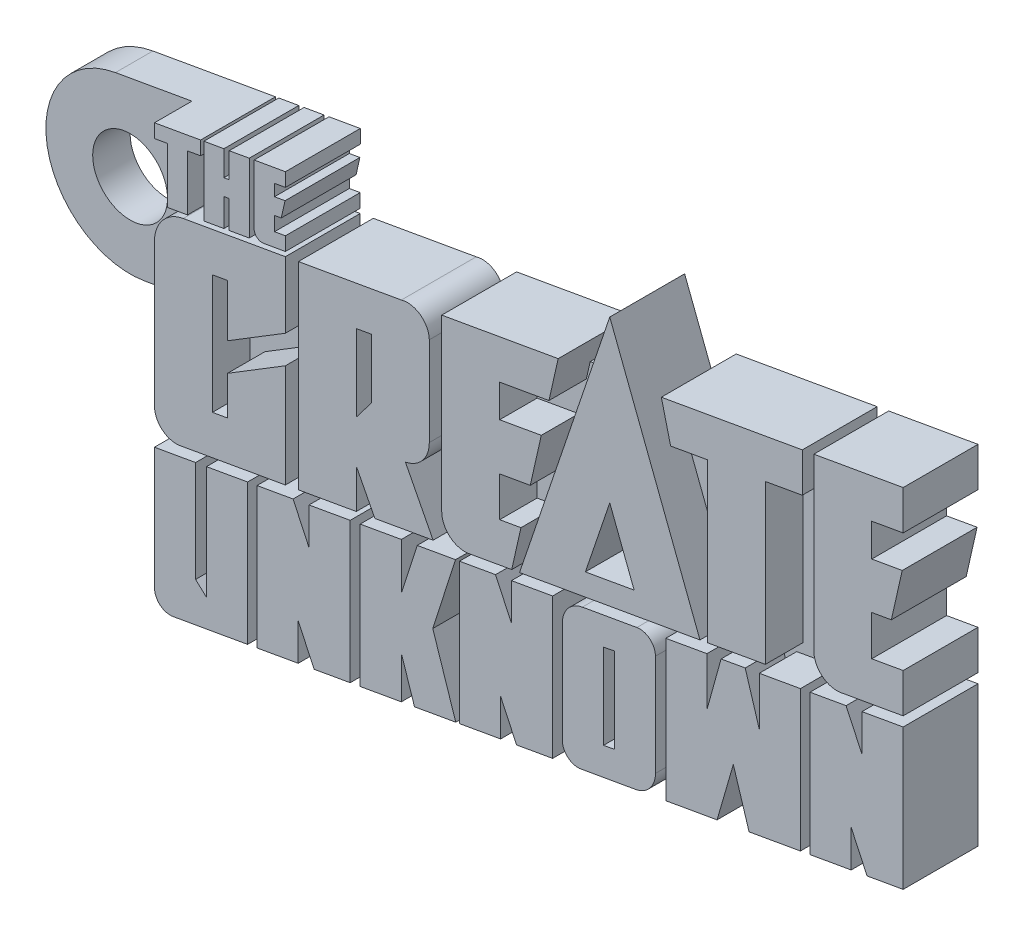
SolidWorks part; units mm, degrees
ref_plane "Front Plane" through (0, 0, 0) normal (0, 0, 1) x (1, 0, 0)
ref_plane "Top Plane" through (0, 0, 0) normal (0, 1, 0) x (1, 0, 0)
ref_plane "Right Plane" through (0, 0, 0) normal (1, 0, 0) x (0, 0, -1)
sketch "Sketch1" plane through (0, 0, 0) normal (0, 0, 1) x (1, 0, 0)
  line L165 (27.5388, 20.4964) -> (27.5388, 15.9483)
  line L166 (27.5388, 15.9483) -> (28.1244, 16.0637)
  line L167 (28.1244, 20.6118) -> (28.1244, 16.0637)
  line L168 (27.5388, 20.4964) -> (28.1244, 20.6118)
  line L169 (8.5269, 18.6309) -> (8.5269, 11.1151)
  line L170 (8.5269, 11.1151) -> (4.5441, 10.4128)
  line L171 (3.5529, 11.2445) -> (3.5529, 17.7538)
  line L172 (3.5529, 17.7538) -> (5.7478, 18.1409)
  line L173 (5.7478, 18.1409) -> (5.7478, 12.7317)
  line L174 (5.7478, 12.7317) -> (6.332, 12.1962)
  line L175 (6.332, 12.1962) -> (6.332, 18.2439)
  line L176 (6.332, 18.2439) -> (8.5269, 18.6309)
  line L177 (14.0078, 12.0815) -> (14.0078, 19.5973)
  line L178 (14.0078, 19.5973) -> (11.8102, 19.2098)
  line L179 (11.8102, 19.2098) -> (11.8102, 17.2332)
  line L180 (11.8102, 17.2332) -> (10.9586, 19.0597)
  line L181 (10.9586, 19.0597) -> (9.0322, 18.72)
  line L182 (9.0322, 18.72) -> (9.0322, 11.2042)
  line L183 (9.0322, 11.2042) -> (11.2298, 11.5917)
  line L184 (11.2298, 11.5917) -> (11.2298, 13.5683)
  line L185 (11.2298, 13.5683) -> (12.0815, 11.7418)
  line L186 (12.0815, 11.7418) -> (14.0078, 12.0815)
  line L187 (18.4217, 16.7978) -> (19.6355, 20.5896)
  line L188 (19.6355, 20.5896) -> (17.5898, 20.2289)
  line L189 (17.5898, 20.2289) -> (16.7417, 17.5794)
  line L190 (16.7417, 17.5794) -> (16.7417, 20.0794)
  line L191 (16.7417, 20.0794) -> (14.5441, 19.6919)
  line L192 (14.5441, 19.6919) -> (14.5441, 12.1761)
  line L193 (14.5441, 12.1761) -> (16.7417, 12.5636)
  line L194 (16.7417, 12.5636) -> (16.7417, 14.8199)
  line L195 (16.7417, 14.8199) -> (17.4448, 12.6875)
  line L196 (17.4448, 12.6875) -> (19.6489, 13.0762)
  line L197 (19.6489, 13.0762) -> (18.4217, 16.7978)
  line L198 (24.8245, 13.9888) -> (24.8245, 21.5046)
  line L199 (24.8245, 21.5046) -> (22.6269, 21.1171)
  line L200 (22.6269, 21.1171) -> (22.6269, 19.1405)
  line L201 (22.6269, 19.1405) -> (21.7752, 20.9669)
  line L202 (21.7752, 20.9669) -> (19.8489, 20.6273)
  line L203 (19.8489, 20.6273) -> (19.8489, 13.1115)
  line L204 (19.8489, 13.1115) -> (22.0465, 13.4989)
  line L205 (22.0465, 13.4989) -> (22.0465, 15.4755)
  line L206 (22.0465, 15.4755) -> (22.8981, 13.6491)
  line L207 (22.8981, 13.6491) -> (24.8245, 13.9888)
  line L208 (30.3195, 16.0433) -> (30.3195, 21.467)
  line L209 (29.3282, 22.2987) -> (26.4129, 21.7847)
  line L210 (25.3438, 20.5106) -> (25.3438, 15.0869)
  line L211 (26.335, 14.2551) -> (29.2504, 14.7692)
  line L212 (35.1142, 23.319) -> (35.8668, 20.8571)
  line L213 (35.8668, 20.8571) -> (35.8668, 23.4517)
  line L214 (35.8668, 23.4517) -> (38.0646, 23.8392)
  line L215 (38.0646, 23.8392) -> (38.0646, 16.3234)
  line L216 (38.0646, 16.3234) -> (35.3221, 15.8398)
  line L217 (35.3221, 15.8398) -> (34.4792, 18.537)
  line L218 (34.4792, 18.537) -> (33.6114, 15.5382)
  line L219 (33.6114, 15.5382) -> (30.871, 15.055)
  line L220 (30.871, 15.055) -> (30.871, 22.5708)
  line L221 (30.871, 22.5708) -> (33.0688, 22.9583)
  line L222 (33.0688, 22.9583) -> (33.0688, 20.3638)
  line L223 (33.0688, 20.3638) -> (33.8253, 23.0917)
  line L224 (33.8253, 23.0917) -> (35.1142, 23.319)
  line L225 (38.5772, 16.4138) -> (38.5772, 23.9296)
  line L226 (38.5772, 23.9296) -> (40.5036, 24.2692)
  line L227 (40.5036, 24.2692) -> (41.3553, 22.4428)
  line L228 (41.3553, 22.4428) -> (41.3553, 24.4194)
  line L229 (41.3553, 24.4194) -> (43.5528, 24.8069)
  line L230 (43.5528, 24.8069) -> (43.5528, 17.2911)
  line L231 (43.5528, 17.2911) -> (41.6265, 16.9514)
  line L232 (41.6265, 16.9514) -> (40.7748, 18.7779)
  line L233 (40.7748, 18.7779) -> (40.7748, 16.8013)
  line L234 (40.7748, 16.8013) -> (38.5772, 16.4138)
  line L235 (38.782, 35.0448) -> (38.782, 25.9457)
  line L236 (43.5528, 25.321) -> (40.2256, 24.7343)
  line L237 (43.5528, 27.4205) -> (43.5528, 25.321)
  line L238 (41.8757, 27.1247) -> (43.5528, 27.4205)
  line L239 (41.8757, 29.2669) -> (41.8757, 27.1247)
  line L240 (42.9229, 29.4516) -> (41.8757, 29.2669)
  line L241 (43.5037, 32.0256) -> (42.9229, 29.4516)
  line L242 (41.8757, 31.7386) -> (43.5037, 32.0256)
  line L243 (41.8757, 33.4908) -> (41.8757, 31.7386)
  line L244 (43.5528, 33.7865) -> (41.8757, 33.4908)
  line L245 (43.5528, 35.886) -> (43.5528, 33.7865)
  line L246 (38.782, 35.0448) -> (43.5528, 35.886)
  line L247 (33.096, 23.4771) -> (33.096, 31.9427)
  line L248 (33.096, 31.9427) -> (31.1296, 31.596)
  line L249 (31.1296, 31.596) -> (30.6338, 33.6081)
  line L250 (30.6338, 33.6081) -> (38.1649, 34.936)
  line L251 (38.1649, 34.936) -> (38.1649, 32.8365)
  line L252 (38.1649, 32.8365) -> (36.1897, 32.4882)
  line L253 (36.1897, 32.4882) -> (36.1897, 24.0226)
  line L254 (36.1897, 24.0226) -> (33.096, 23.4771)
  line L255 (26.575, 23.4945) -> (27.8781, 27.3418)
  line L256 (27.8781, 27.3418) -> (29.1808, 23.954)
  line L257 (29.1808, 23.954) -> (26.575, 23.4945)
  line L258 (27.8781, 35.9396) -> (23.0573, 21.707)
  line L259 (23.0573, 21.707) -> (32.6975, 23.4069)
  line L260 (32.6975, 23.4069) -> (27.8781, 35.9396)
  line L261 (15.1429, 28.7771) -> (15.1429, 25.594)
  line L262 (15.1429, 25.594) -> (14.3363, 24.5351)
  line L263 (14.3363, 24.5351) -> (14.3363, 28.6349)
  line L264 (14.3363, 28.6349) -> (15.1429, 28.7771)
  line L265 (18.9009, 22.4401) -> (18.9009, 31.5392)
  line L266 (18.9009, 31.5392) -> (25.1218, 32.6361)
  line L267 (25.1218, 32.6361) -> (24.6284, 30.4496)
  line L268 (24.6284, 30.4496) -> (21.9947, 29.9852)
  line L269 (21.9947, 29.9852) -> (21.9947, 28.2446)
  line L270 (21.9947, 28.2446) -> (24.2193, 28.6369)
  line L271 (24.2193, 28.6369) -> (23.6304, 26.0272)
  line L272 (23.6304, 26.0272) -> (21.9947, 25.7388)
  line L273 (21.9947, 25.7388) -> (21.9947, 23.6192)
  line L274 (21.9947, 23.6192) -> (23.1323, 23.8198)
  line L275 (23.1323, 23.8198) -> (22.6388, 21.6333)
  line L276 (22.6388, 21.6333) -> (21.9947, 21.5197)
  line L277 (21.9947, 21.5197) -> (20.3446, 21.2287)
  line L278 (11.2426, 30.1889) -> (11.2426, 19.6238)
  line L279 (11.2426, 19.6238) -> (14.3363, 20.1693)
  line L280 (14.3363, 20.1693) -> (14.3363, 22.2688)
  line L281 (14.3363, 22.2688) -> (15.3279, 20.3441)
  line L282 (15.3279, 20.3441) -> (18.4403, 20.8929)
  line L283 (18.4403, 20.8929) -> (16.9577, 23.7709)
  line L284 (18.2366, 25.3109) -> (18.2366, 30.0662)
  line L285 (16.7417, 31.1585) -> (11.2426, 30.1889)
  line L286 (8.8762, 33.7042) -> (8.8762, 30.5234)
  line L287 (9.381, 30.0998) -> (10.5468, 30.3053)
  line L288 (10.5468, 30.3053) -> (10.5468, 31.0325)
  line L289 (10.5468, 31.0325) -> (9.9645, 30.9298)
  line L290 (9.9645, 30.9298) -> (9.9645, 31.6825)
  line L291 (9.9645, 31.6825) -> (10.3249, 31.7461)
  line L292 (10.3249, 31.7461) -> (10.5283, 32.6476)
  line L293 (10.5283, 32.6476) -> (9.9645, 32.5482)
  line L294 (9.9645, 32.5482) -> (9.9645, 33.1689)
  line L295 (9.9645, 33.1689) -> (10.5487, 33.2719)
  line L296 (10.5487, 33.2719) -> (10.5487, 33.9991)
  line L297 (10.5487, 33.9991) -> (8.8762, 33.7042)
  line L298 (6.1925, 33.231) -> (6.1925, 29.5376)
  line L299 (6.1925, 29.5376) -> (7.2626, 29.7262)
  line L300 (7.2626, 29.7262) -> (7.2626, 31.2058)
  line L301 (7.2626, 31.2058) -> (7.5462, 31.2558)
  line L302 (7.5462, 31.2558) -> (7.5462, 29.7762)
  line L303 (7.5462, 29.7762) -> (8.6163, 29.9649)
  line L304 (8.6163, 29.9649) -> (8.6163, 33.6584)
  line L305 (8.6163, 33.6584) -> (7.5462, 33.4697)
  line L306 (7.5462, 33.4697) -> (7.5462, 32.128)
  line L307 (7.5462, 32.128) -> (7.2626, 32.078)
  line L308 (7.2626, 32.078) -> (7.2626, 33.4197)
  line L309 (7.2626, 33.4197) -> (6.1925, 33.231)
  line L310 (4.2501, 32.1569) -> (4.2501, 29.1951)
  line L311 (4.2501, 29.1951) -> (5.3202, 29.3837)
  line L312 (5.3202, 29.3837) -> (5.3202, 32.3456)
  line L313 (5.3202, 32.3456) -> (6.0168, 32.4685)
  line L314 (6.0168, 32.4685) -> (6.0168, 33.2)
  line L315 (6.0168, 33.2) -> (3.5529, 32.7655)
  line L316 (3.5529, 32.7655) -> (3.5529, 32.034)
  line L317 (3.5529, 32.034) -> (4.2501, 32.1569)
  line L318 (3.5529, 19.6594) -> (3.5529, 27.2755)
  line L319 (5.0867, 29.1034) -> (10.5468, 30.0662)
  line L320 (10.5468, 30.0662) -> (10.5468, 26.5235)
  line L321 (10.5468, 26.5235) -> (7.453, 24.6277)
  line L322 (7.453, 24.6277) -> (7.453, 27.4212)
  line L323 (7.453, 27.4212) -> (6.6466, 27.279)
  line L324 (6.6466, 27.279) -> (6.6466, 20.9129)
  line L325 (6.6466, 20.9129) -> (7.453, 21.0551)
  line L326 (7.453, 21.0551) -> (7.453, 23.1225)
  line L327 (7.453, 23.1225) -> (10.5468, 25.0183)
  line L328 (10.5468, 25.0183) -> (10.5468, 19.5011)
  line L329 (10.5468, 19.5011) -> (4.9232, 18.5095)
  arc A12 (3.5529, 11.2445) -> (4.5441, 10.4128) centre (4.3975, 11.2445) ccw
  arc A13 (30.3195, 21.467) -> (29.3282, 22.2987) centre (29.4749, 21.467) ccw
  arc A14 (26.4129, 21.7847) -> (25.3438, 20.5106) centre (26.6375, 20.5106) ccw
  arc A15 (25.3438, 15.0869) -> (26.335, 14.2551) centre (26.1884, 15.0869) ccw
  arc A16 (29.2504, 14.7692) -> (30.3195, 16.0433) centre (29.0258, 16.0433) ccw
  arc A17 (38.782, 25.9457) -> (40.2256, 24.7343) centre (40.012, 25.9457) ccw
  arc A18 (18.9009, 22.4401) -> (20.3446, 21.2287) centre (20.131, 22.4401) ccw
  arc A19 (16.9577, 23.7709) -> (18.2366, 25.3109) centre (16.6699, 25.3109) ccw
  arc A20 (18.2366, 30.0662) -> (16.7417, 31.1585) centre (17.0693, 30.0378) ccw
  arc A21 (8.8762, 30.5234) -> (9.381, 30.0998) centre (9.3063, 30.5234) ccw
  arc A22 (5.0867, 29.1034) -> (3.5529, 27.2755) centre (5.4091, 27.2755) ccw
  arc A23 (3.5529, 19.6594) -> (4.9232, 18.5095) centre (4.7205, 19.6594) ccw
  point P2 (0, 0)
extrude "Boss-Extrude1" add sketch "Sketch1" along normal blind 2
sketch "Sketch3" plane through (0, 0, 0) normal (0, 0, -1) x (-1, 0, 0)
  line L0 (-38.5772, 16.4138) -> (-38.5772, 23.9296) construction
  line L1 (-7.5462, 32.9346) -> (-7.2626, 32.8846)
  line L2 (-6.629, 33.3079) -> (-6.629, 32.7729) construction
  line L3 (-4.2501, 31.7461) -> (-4.7852, 31.7461) construction
  line L4 (-41.3553, 24.4194) -> (-43.5528, 24.8069) construction
  line L5 (-43.5528, 24.8069) -> (-43.5528, 17.2911) construction
  line L6 (-43.5528, 17.2911) -> (-41.6265, 16.9514) construction
  line L7 (-41.6265, 16.9514) -> (-40.7748, 18.7779) construction
  line L8 (-40.7748, 18.7779) -> (-40.7748, 16.8013) construction
  line L9 (-40.7748, 16.8013) -> (-38.5772, 16.4138) construction
  line L10 (-38.0646, 23.8392) -> (-38.0646, 16.3234) construction
  line L11 (-38.0646, 16.3234) -> (-35.3221, 15.8398) construction
  line L12 (-35.3221, 15.8398) -> (-34.4792, 18.537) construction
  line L13 (-34.4792, 18.537) -> (-33.6114, 15.5382) construction
  line L14 (-33.6114, 15.5382) -> (-30.871, 15.055) construction
  line L15 (-30.871, 15.055) -> (-30.871, 22.5708) construction
  line L16 (-1.0316, 23.1821) -> (-3.5529, 23.6267)
  line L17 (0.5313, 32.0454) -> (-3.5529, 32.7655)
  line L18 (-0.2501, 27.6137) -> (-4.2501, 27.6137) construction
  line L19 (-4.2501, 32.1569) -> (-4.2501, 29.1951) construction
  line L23 (-25.3438, 20.5106) -> (-25.3438, 15.0869) construction
  line L24 (-26.335, 14.2551) -> (-29.2504, 14.7692) construction
  line L25 (-30.3195, 16.0433) -> (-30.3195, 21.467) construction
  line L27 (-19.8489, 20.6273) -> (-19.8489, 13.1115) construction
  line L28 (-19.8489, 13.1115) -> (-22.0465, 13.4989) construction
  line L29 (-22.0465, 13.4989) -> (-22.0465, 15.4755) construction
  line L30 (-22.0465, 15.4755) -> (-22.8981, 13.6491) construction
  line L31 (-22.8981, 13.6491) -> (-24.8245, 13.9888) construction
  line L32 (-24.8245, 13.9888) -> (-24.8245, 21.5046) construction
  line L37 (-14.5441, 19.6919) -> (-14.5441, 12.1761) construction
  line L38 (-14.5441, 12.1761) -> (-16.7417, 12.5636) construction
  line L39 (-16.7417, 12.5636) -> (-16.7417, 14.8199) construction
  line L40 (-16.7417, 14.8199) -> (-17.4448, 12.6875) construction
  line L41 (-17.4448, 12.6875) -> (-19.6489, 13.0762) construction
  line L42 (-19.6489, 13.0762) -> (-18.4217, 16.7978) construction
  line L48 (-9.0322, 18.72) -> (-9.0322, 11.2042) construction
  line L49 (-9.0322, 11.2042) -> (-11.2298, 11.5917) construction
  line L50 (-11.2298, 11.5917) -> (-11.2298, 13.5683) construction
  line L51 (-11.2298, 13.5683) -> (-12.0815, 11.7418) construction
  line L52 (-12.0815, 11.7418) -> (-14.0078, 12.0815) construction
  line L53 (-14.0078, 12.0815) -> (-14.0078, 19.5973) construction
  line L60 (-8.5269, 18.6309) -> (-8.5269, 11.1151) construction
  line L61 (-8.5269, 11.1151) -> (-4.5441, 10.4128) construction
  line L62 (-3.5529, 11.2445) -> (-3.5529, 17.7538) construction
  line L63 (-3.5529, 17.7538) -> (-5.7478, 18.1409) construction
  line L68 (-6.0168, 32.4685) -> (-6.0168, 33.2) construction
  line L69 (-6.0168, 33.2) -> (-3.5529, 32.7655) construction
  line L74 (-8.6163, 29.9649) -> (-8.6163, 33.6584) construction
  line L75 (-8.6163, 33.6584) -> (-7.5462, 33.4697) construction
  line L76 (-7.5462, 33.4697) -> (-7.5462, 32.128) construction
  line L78 (-7.2626, 32.078) -> (-7.2626, 33.4197) construction
  line L79 (-7.2626, 33.4197) -> (-6.1925, 33.231) construction
  line L80 (-6.1925, 33.231) -> (-6.1925, 29.5376) construction
  line L86 (-8.8762, 33.7042) -> (-8.8762, 30.5234) construction
  line L87 (-9.381, 30.0998) -> (-10.5468, 30.3053) construction
  line L88 (-10.5468, 30.3053) -> (-10.5468, 31.0325) construction
  line L89 (-10.5468, 31.0325) -> (-9.9645, 30.9298) construction
  line L90 (-9.9645, 30.9298) -> (-9.9645, 31.6825) construction
  line L91 (-9.9645, 31.6825) -> (-10.3249, 31.7461) construction
  line L92 (-10.3249, 31.7461) -> (-10.5283, 32.6476) construction
  line L93 (-10.5283, 32.6476) -> (-9.9645, 32.5482) construction
  line L94 (-9.9645, 32.5482) -> (-9.9645, 33.1689) construction
  line L95 (-9.9645, 33.1689) -> (-10.5487, 33.2719) construction
  line L96 (-10.5487, 33.2719) -> (-10.5487, 33.9991) construction
  line L97 (-10.5487, 33.9991) -> (-8.8762, 33.7042) construction
  line L101 (-3.5529, 19.6594) -> (-3.5529, 27.2755) construction
  line L102 (-5.0867, 29.1034) -> (-10.5468, 30.0662) construction
  line L103 (-10.5468, 30.0662) -> (-10.5468, 26.5235) construction
  line L111 (-16.7417, 31.1585) -> (-11.2426, 30.1889) construction
  line L112 (-11.2426, 30.1889) -> (-11.2426, 19.6238) construction
  line L119 (-5.3202, 31.3658) -> (-5.3202, 29.3837) construction
  line L120 (-25.3438, 15.3127) -> (-41.8757, 18.2277) construction
  line L121 (-18.9009, 31.5392) -> (-25.1218, 32.6361) construction
  line L122 (-25.1218, 32.6361) -> (-24.6284, 30.4496) construction
  line L133 (-18.9009, 22.4401) -> (-18.9009, 31.5392) construction
  line L134 (-32.6975, 23.4069) -> (-27.8781, 35.9396) construction
  line L135 (-27.8781, 35.9396) -> (-23.0573, 21.707) construction
  line L137 (-30.6338, 33.6081) -> (-38.1649, 34.936) construction
  line L138 (-38.1649, 34.936) -> (-38.1649, 32.8365) construction
  line L144 (-31.1296, 31.596) -> (-30.6338, 33.6081) construction
  line L145 (-38.782, 35.0448) -> (-43.5528, 35.886) construction
  line L146 (-43.5528, 35.886) -> (-43.5528, 33.7865) construction
  line L147 (-43.5528, 33.7865) -> (-41.8757, 33.4908) construction
  line L148 (-41.8757, 33.4908) -> (-41.8757, 31.7386) construction
  line L149 (-41.8757, 31.7386) -> (-43.5037, 32.0256) construction
  line L150 (-43.5037, 32.0256) -> (-42.9229, 29.4516) construction
  line L151 (-42.9229, 29.4516) -> (-41.8757, 29.2669) construction
  line L152 (-41.8757, 29.2669) -> (-41.8757, 27.1247) construction
  line L153 (-41.8757, 27.1247) -> (-43.5528, 27.4205) construction
  line L154 (-43.5528, 27.4205) -> (-43.5528, 25.321) construction
  line L155 (-43.5528, 25.321) -> (-40.2256, 24.7343) construction
  line L156 (-38.782, 35.0448) -> (-38.782, 25.9457) construction
  line L157 (-38.5772, 16.4138) -> (-38.5772, 17.6461)
  line L161 (-41.8757, 24.5112) -> (-43.5528, 24.8069)
  line L162 (-43.5528, 24.8069) -> (-43.5528, 17.2911)
  line L163 (-43.5528, 17.2911) -> (-41.6265, 16.9514)
  line L164 (-41.6265, 16.9514) -> (-40.7748, 18.7779)
  line L165 (-40.7748, 18.7779) -> (-40.7748, 16.8013)
  line L166 (-40.7748, 16.8013) -> (-38.5772, 16.4138)
  line L167 (-38.0646, 17.5557) -> (-38.0646, 16.3234)
  line L168 (-38.0646, 16.3234) -> (-35.3221, 15.8398)
  line L169 (-35.3221, 15.8398) -> (-34.4792, 18.537)
  line L170 (-34.4792, 18.537) -> (-33.6114, 15.5382)
  line L171 (-33.6114, 15.5382) -> (-30.871, 15.055)
  line L172 (-30.871, 15.055) -> (-30.871, 16.2873)
  line L180 (-25.3438, 15.3127) -> (-25.3438, 15.0869)
  line L181 (-26.335, 14.2551) -> (-29.2504, 14.7692)
  line L182 (-30.3195, 16.0433) -> (-30.3195, 16.19)
  line L184 (-19.8489, 14.3438) -> (-19.8489, 13.1115)
  line L185 (-19.8489, 13.1115) -> (-22.0465, 13.4989)
  line L186 (-22.0465, 13.4989) -> (-22.0465, 15.4755)
  line L187 (-22.0465, 15.4755) -> (-22.8981, 13.6491)
  line L188 (-22.8981, 13.6491) -> (-24.8245, 13.9888)
  line L189 (-24.8245, 13.9888) -> (-24.8245, 15.2211)
  line L194 (-14.5441, 13.4084) -> (-14.5441, 12.1761)
  line L195 (-14.5441, 12.1761) -> (-16.7417, 12.5636)
  line L196 (-16.7417, 12.5636) -> (-16.7417, 14.8199)
  line L197 (-16.7417, 14.8199) -> (-17.4448, 12.6875)
  line L198 (-17.4448, 12.6875) -> (-19.6489, 13.0762)
  line L199 (-19.6489, 13.0762) -> (-19.2648, 14.2408)
  line L205 (-9.0322, 12.4365) -> (-9.0322, 11.2042)
  line L206 (-9.0322, 11.2042) -> (-11.2298, 11.5917)
  line L207 (-11.2298, 11.5917) -> (-11.2298, 13.5683)
  line L208 (-11.2298, 13.5683) -> (-12.0815, 11.7418)
  line L209 (-12.0815, 11.7418) -> (-14.0078, 12.0815)
  line L210 (-14.0078, 12.0815) -> (-14.0078, 13.3138)
  line L217 (-8.5269, 12.3474) -> (-8.5269, 11.1151)
  line L218 (-8.5269, 11.1151) -> (-4.5441, 10.4128)
  line L219 (-3.5529, 11.2445) -> (-3.5529, 17.7538)
  line L220 (-3.5529, 17.7538) -> (-4.7852, 17.9711)
  line L225 (-6.0168, 32.6649) -> (-6.0168, 33.2)
  line L226 (-6.0168, 33.2) -> (-3.5529, 32.7655)
  line L231 (-8.6163, 33.1233) -> (-8.6163, 33.6584)
  line L232 (-8.6163, 33.6584) -> (-7.5462, 33.4697)
  line L233 (-7.5462, 33.4697) -> (-7.5462, 32.9346)
  line L235 (-7.2626, 32.8846) -> (-7.2626, 33.4197)
  line L236 (-7.2626, 33.4197) -> (-6.1925, 33.231)
  line L237 (-6.1925, 33.231) -> (-6.1925, 32.6959)
  line L243 (-8.8762, 33.7042) -> (-8.8762, 33.1691)
  line L244 (-9.9645, 30.2027) -> (-10.5468, 30.3053)
  line L245 (-10.5468, 30.3053) -> (-10.5468, 31.0325)
  line L246 (-10.5468, 31.0325) -> (-9.9645, 30.9298)
  line L247 (-9.9645, 30.9298) -> (-9.9645, 31.6825)
  line L248 (-9.9645, 31.6825) -> (-10.3249, 31.7461)
  line L249 (-10.3249, 31.7461) -> (-10.5283, 32.6476)
  line L250 (-10.5283, 32.6476) -> (-9.9645, 32.5482)
  line L251 (-9.9645, 32.5482) -> (-9.9645, 33.1689)
  line L252 (-9.9645, 33.1689) -> (-10.5487, 33.2719)
  line L253 (-10.5487, 33.2719) -> (-10.5487, 33.9991)
  line L254 (-10.5487, 33.9991) -> (-8.8762, 33.7042)
  line L258 (-3.5529, 19.6594) -> (-3.5529, 23.6267)
  line L259 (-9.9645, 29.9635) -> (-10.5468, 30.0662)
  line L260 (-10.5468, 30.0662) -> (-10.5468, 28.8339)
  line L268 (-16.7417, 31.1585) -> (-11.2426, 30.1889)
  line L269 (-11.2426, 30.1889) -> (-11.2426, 28.9566)
  line L278 (-18.9009, 31.5392) -> (-25.1218, 32.6361)
  line L279 (-25.1218, 32.6361) -> (-24.8322, 31.3528)
  line L290 (-18.9009, 30.3069) -> (-18.9009, 31.5392)
  line L291 (-29.3365, 32.147) -> (-27.8781, 35.9396)
  line L292 (-27.8781, 35.9396) -> (-26.4192, 31.6326)
  line L294 (-30.6338, 33.6081) -> (-38.1649, 34.936)
  line L295 (-38.1649, 34.936) -> (-38.1649, 33.7037)
  line L301 (-30.9248, 32.4271) -> (-30.6338, 33.6081)
  line L302 (-38.782, 35.0448) -> (-43.5528, 35.886)
  line L303 (-43.5528, 35.886) -> (-43.5528, 33.7865)
  line L304 (-43.5528, 33.7865) -> (-41.8757, 33.4908)
  line L305 (-41.8757, 33.4908) -> (-41.8757, 31.7386)
  line L306 (-41.8757, 31.7386) -> (-43.5037, 32.0256)
  line L307 (-43.5037, 32.0256) -> (-42.9229, 29.4516)
  line L308 (-42.9229, 29.4516) -> (-41.8757, 29.2669)
  line L309 (-41.8757, 29.2669) -> (-41.8757, 27.1247)
  line L310 (-41.8757, 27.1247) -> (-43.5528, 27.4205)
  line L311 (-43.5528, 27.4205) -> (-43.5528, 25.321)
  line L312 (-43.5528, 25.321) -> (-41.8757, 25.0252)
  line L313 (-38.782, 35.0448) -> (-38.782, 33.8125)
  line L314 (-41.8757, 34.358) -> (-9.9645, 28.7312) construction
  line L315 (-9.9645, 28.7312) -> (-9.9645, 33.361) construction
  line L316 (-9.9645, 33.361) -> (-4.7852, 32.4478) construction
  line L317 (-4.7852, 32.4478) -> (-4.7852, 11.6876) construction
  line L318 (-4.7852, 11.6876) -> (-25.3438, 15.3127) construction
  line L319 (-41.8757, 18.2277) -> (-41.8757, 34.358) construction
  line L320 (-30.871, 16.2873) -> (-30.3113, 16.1886)
  line L321 (-25.3438, 15.3127) -> (-24.8245, 15.2211)
  line L322 (-19.8489, 14.3438) -> (-19.2648, 14.2408)
  line L323 (-14.5441, 13.4084) -> (-14.0078, 13.3138)
  line L324 (-9.0322, 12.4365) -> (-8.5269, 12.3474)
  line L325 (-4.7852, 18.4936) -> (-4.7852, 17.9711)
  line L327 (-6.0168, 32.6649) -> (-6.1925, 32.6959)
  line L328 (-8.6163, 33.1233) -> (-8.8762, 33.1691)
  line L329 (-9.9645, 30.2027) -> (-9.9645, 29.9635)
  line L330 (-10.5468, 28.8339) -> (-11.2426, 28.9566)
  line L331 (-18.2272, 30.1881) -> (-18.9009, 30.3069)
  line L332 (-24.8322, 31.3528) -> (-26.4192, 31.6326)
  line L333 (-29.3365, 32.147) -> (-30.9248, 32.4271)
  line L334 (-38.782, 33.8125) -> (-38.1649, 33.7037)
  line L335 (-41.8757, 25.0252) -> (-41.8757, 24.5112)
  line L336 (-14.6099, 30.7826) -> (-14.6099, 29.5503) construction
  line L337 (-12.7842, 11.8658) -> (-12.7842, 13.0981) construction
  line L338 (-3.5529, 26.0088) -> (-4.7852, 26.0088) construction
  line L339 (-4.2501, 31.3658) -> (-5.3202, 31.3658) construction
  line L340 (-38.5772, 17.6461) -> (-38.0646, 17.5557)
  arc A0 (-26.335, 14.2551) -> (-25.3438, 15.0869) centre (-26.1884, 15.0869) ccw construction
  arc A1 (-30.3195, 16.0433) -> (-29.2504, 14.7692) centre (-29.0258, 16.0433) ccw construction
  arc A2 (-1.0316, 23.1821) -> (0.5313, 32.0454) centre (-0.2501, 27.6137) ccw
  circle A3 centre (-0.2501, 27.6137) radius 2
  arc A4 (-4.5441, 10.4128) -> (-3.5529, 11.2445) centre (-4.3975, 11.2445) ccw construction
  arc A6 (-4.9232, 18.5095) -> (-3.5529, 19.6594) centre (-4.7205, 19.6594) ccw construction
  arc A8 (-16.7417, 31.1585) -> (-18.2366, 30.0662) centre (-17.0693, 30.0378) ccw construction
  arc A12 (-26.335, 14.2551) -> (-25.3438, 15.0869) centre (-26.1884, 15.0869) ccw
  arc A13 (-30.3195, 16.0433) -> (-29.2504, 14.7692) centre (-29.0258, 16.0433) ccw
  arc A16 (-4.5441, 10.4128) -> (-3.5529, 11.2445) centre (-4.3975, 11.2445) ccw
  arc A18 (-4.7852, 18.4936) -> (-3.5529, 19.6594) centre (-4.7205, 19.6594) ccw
  arc A20 (-16.7417, 31.1585) -> (-18.2272, 30.1881) centre (-17.0693, 30.0378) ccw
  point P42 (-4.3975, 27.6397)
  point P58 (-1.8397, 26.3709)
  point P59 (-4.5441, 27.6653)
  point P94 (-4.7852, 31.3658)
  dimension "D1" = 4
  dimension "D2" = 2.5
  dimension "D3" = 4
extrude "Boss-Extrude2" add sketch "Sketch3" along normal blind 2
